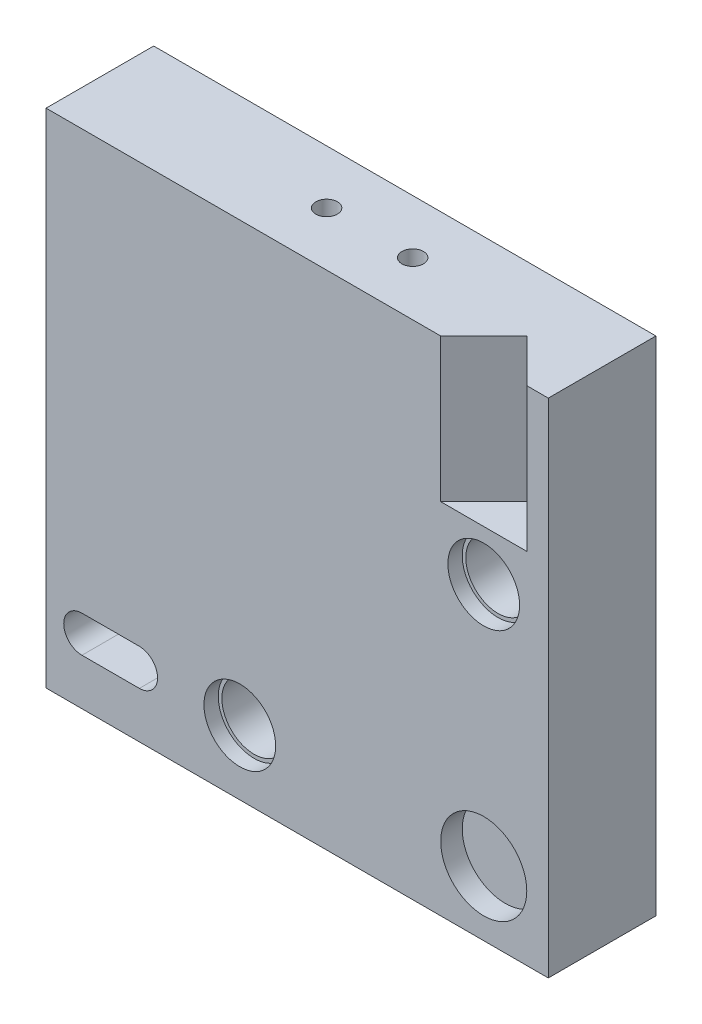
SolidWorks part; units mm, degrees
ref_plane "Front Plane" through (0, 0, 0) normal (0, 0, 1) x (1, 0, 0)
ref_plane "Top Plane" through (0, 0, 0) normal (0, 1, 0) x (1, 0, 0)
ref_plane "Right Plane" through (0, 0, 0) normal (1, 0, 0) x (0, 0, -1)
sketch "Sketch1" plane through (0, 0, 0) normal (0, 0, 1) x (1, 0, 0)
  line L1 (-17.7337, 13.9901) -> (17.2663, 13.9901)
  line L2 (-17.7337, 13.9901) -> (-17.7337, -21.0099)
  line L3 (-17.7337, -21.0099) -> (17.2663, -21.0099)
  line L4 (17.2663, 13.9901) -> (17.2663, -21.0099)
  dimension "D1" = 35
  dimension "D2" = 35
extrude "Boss-Extrude1" add sketch "Sketch1" along normal blind 7.5
sketch "Sketch2" plane through (0, 0, 0) normal (0, 0, -1) x (-1, 0, 0)
  line L0 (17.7337, 2.9901) -> (-6.2663, 2.9901)
  line L1 (17.7337, 13.9901) -> (17.7337, -21.0099) construction
  line L2 (-6.2663, 2.9901) -> (-6.2663, -10.0099)
  line L3 (-6.2663, -10.0099) -> (17.7337, -10.0099)
  line L4 (-17.2663, 13.9901) -> (17.7337, 13.9901) construction
  line L6 (-17.2663, -21.0099) -> (-17.2663, 13.9901) construction
  line L7 (17.7337, 2.9901) -> (17.7337, -10.0099)
  dimension "D1" = 13
  dimension "D2" = 11
  dimension "D3" = 11
extrude "Cut-Extrude2" cut sketch "Sketch2" against normal blind 5
sketch "Sketch4" plane through (0, 0, 7.5) normal (0, 0, 1) x (1, 0, 0)
  line L0 (-17.7337, 13.9901) -> (-17.7337, -21.0099) construction
  line L1 (-17.7337, -21.0099) -> (17.2663, -21.0099) construction
  line L3 (-11.2337, -15.2399) -> (-15.2337, -15.2399)
  line L5 (-11.2337, -17.7799) -> (-15.2337, -17.7799)
  line L7 (-11.2337, -15.2399) -> (-15.2337, -17.7799) construction
  line L8 (-11.2337, -17.7799) -> (-15.2337, -15.2399) construction
  arc A0 (-15.2337, -15.2399) -> (-15.2337, -17.7799) centre (-15.2337, -16.5099) ccw
  arc A1 (-11.2337, -15.2399) -> (-11.2337, -17.7799) centre (-11.2337, -16.5099) cw
  point P0 (-13.2337, -16.5099)
  dimension "D3" = 4
  dimension "D1" = 4.5
  dimension "D2" = 4.5
  dimension "D4" = 2.54
sketch "Sketch5" plane through (0, 0, 7.5) normal (0, 0, 1) x (1, 0, 0)
  line L0 (-17.7337, -21.0099) -> (17.2663, -21.0099) construction
  line L1 (17.2663, -21.0099) -> (17.2663, 13.9901) construction
  circle A0 centre (12.7663, 0.4901) radius 2.5
  circle A1 centre (-4.2337, -16.5099) radius 2.5
  dimension "D5" = 5
  dimension "D6" = 5
  dimension "D1" = 21.5
  dimension "D2" = 21.5
  dimension "D3" = 4.5
  dimension "D4" = 4.5
sketch "Sketch10" plane through (0, 13.9901, 0) normal (0, 1, 0) x (1, 0, 0)
  line L0 (17.2663, -7.5) -> (17.2663, 0) construction
  line L1 (17.2663, 0) -> (-17.7337, 0) construction
  line L2 (17.2663, -7.5) -> (-17.7337, -7.5) construction
  circle A0 centre (4.0663, -3.75) radius 0.75
  circle A1 centre (-1.9337, -3.75) radius 0.75
  dimension "D1" = 13.2
  dimension "D2" = 1.5
  dimension "D3" = 1.5
  dimension "D4" = 3.75
  dimension "D5" = 3.75
  dimension "D6" = 6
extrude "Cut-Extrude7" cut sketch "Sketch10" against normal blind 7
extrude "Cut-Extrude11" cut sketch "Sketch5" against normal blind 1
sketch "Sketch11" plane through (0, 0, 6.5) normal (0, 0, 1) x (1, 0, 0)
  circle A0 centre (-4.2337, -16.5099) radius 2.25
  circle A1 centre (12.7663, 0.4901) radius 2.25
  dimension "D1" = 4.5
  dimension "D2" = 4.5
extrude "Cut-Extrude12" cut sketch "Sketch11" against normal blind 5
sketch "Sketch13" plane through (0, -21.0099, 0) normal (0, -1, 0) x (1, 0, 0)
  line L0 (9.7663, 7.5) -> (12.7663, 4.5)
  line L1 (-17.7337, 7.5) -> (17.2663, 7.5) construction
  line L2 (12.7663, 4.5) -> (15.7663, 7.5)
  line L3 (17.2663, 7.5) -> (17.2663, 0) construction
  line L4 (9.7663, 7.5) -> (15.7663, 7.5)
  dimension "D1" = 3
  dimension "D2" = 135
  dimension "D3" = 4.5
extrude "Cut-Extrude13" cut sketch "Sketch13" against normal blind 10
sketch "Sketch15" plane through (0, 13.9901, 0) normal (0, 1, 0) x (1, 0, 0)
  line L0 (9.7663, -7.5) -> (12.7663, -4.5)
  line L1 (17.2663, -7.5) -> (-17.7337, -7.5) construction
  line L2 (12.7663, -4.5) -> (15.7663, -7.5)
  line L3 (9.7663, -7.5) -> (15.7663, -7.5)
  dimension "D1" = 0
  dimension "D2" = 0
  dimension "D3" = 0
extrude "Cut-Extrude14" cut sketch "Sketch15" against normal blind 10
extrude "Cut-Extrude15" cut sketch "Sketch4" against normal blind 4
sketch "Sketch16" plane through (0, -11.0099, 0) normal (0, -1, 0) x (-1, 0, 0)
  line L0 (-9.7663, -7.5) -> (-15.7663, -7.5)
  line L1 (-15.7663, -7.5) -> (-9.7663, -7.5) construction
  line L2 (-15.7663, -7.5) -> (-12.7663, -4.5)
  line L3 (-12.7663, -4.5) -> (-15.7663, -7.5) construction
  line L4 (-12.7663, -4.5) -> (-9.7663, -7.5)
extrude "Boss-Extrude2" add sketch "Sketch16" along normal blind 10
sketch "Sketch17" plane through (0, 0, 7.5) normal (0, 0, 1) x (1, 0, 0)
  line L0 (-17.7337, -21.0099) -> (17.2663, -21.0099) construction
  line L1 (17.2663, -21.0099) -> (17.2663, 13.9901) construction
  circle A0 centre (12.7663, -16.5099) radius 3
  dimension "D1" = 6
  dimension "D2" = 4.5
  dimension "D3" = 4.5
extrude "Cut-Extrude16" cut sketch "Sketch17" against normal blind 1.5
